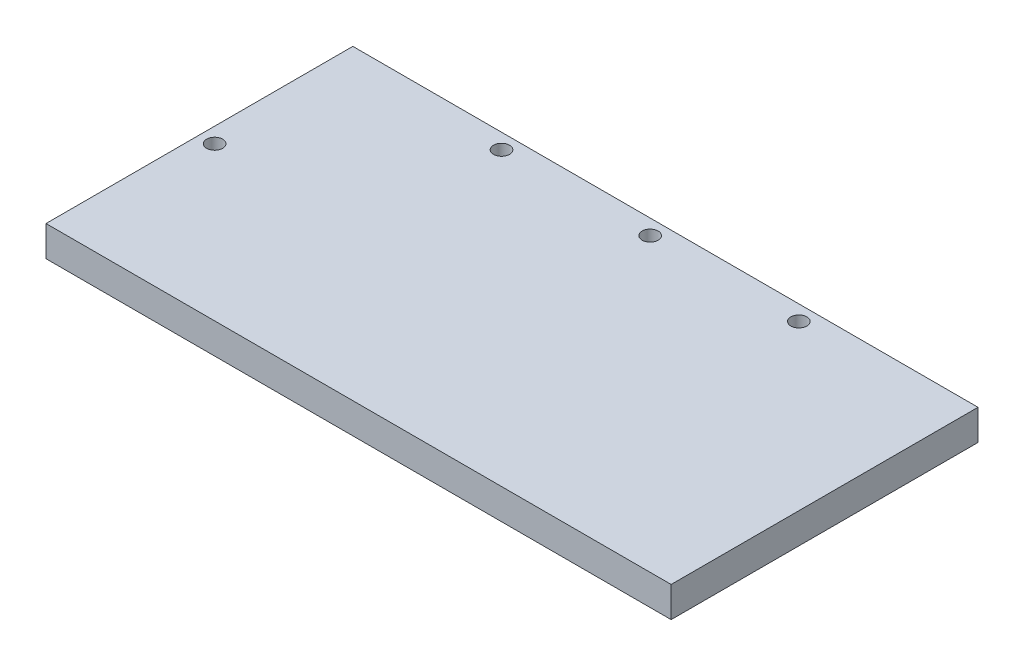
SolidWorks part; units mm, degrees
ref_plane "Front Plane" through (0, 0, 0) normal (0, 0, 1) x (1, 0, 0)
ref_plane "Top Plane" through (0, 0, 0) normal (0, 1, 0) x (1, 0, 0)
ref_plane "Right Plane" through (0, 0, 0) normal (1, 0, 0) x (0, 0, -1)
sketch "Sketch1" plane through (0, 0, 0) normal (0, 1, 0) x (1, 0, 0)
  line L0 (0, 40.25) -> (0, -40.25) construction
  line L1 (-82, 40.25) -> (82, 40.25)
  line L2 (-82, 40.25) -> (-82, -40.25)
  line L3 (-82, -40.25) -> (82, -40.25)
  line L4 (82, 40.25) -> (82, -40.25)
  line L5 (-82, 40.25) -> (82, -40.25) construction
  line L6 (-82, -40.25) -> (82, 40.25) construction
  line L7 (-82, 40.25) -> (-74, 40.25)
  line L8 (-82, 40.25) -> (-82, -40.25)
  line L9 (-82, -40.25) -> (-74, -40.25)
  line L10 (-74, 40.25) -> (-74, -40.25)
  line L11 (74, 36.25) -> (-74, 36.25) construction
  line L12 (-74, 40.25) -> (74, 40.25)
  line L13 (-74, 40.25) -> (-74, 32.25)
  line L14 (-74, 32.25) -> (74, 32.25)
  line L15 (74, 40.25) -> (74, 32.25)
  line L16 (-82, 0) -> (-74, 0) construction
  circle A0 centre (0, 36.25) radius 2.1
  circle A1 centre (39, 36.25) radius 2.1
  circle A2 centre (-39, 36.25) radius 2.1
  circle A3 centre (-78, 0) radius 2.1
  point P0 (0, 0)
  point P10 (-82, 0)
  point P11 (-74, 0)
  dimension "D6" = 4.2
  dimension "D9" = 4.2
  dimension "D1" = 80.5
  dimension "D2" = 164
  dimension "D3" = 8
  dimension "D4" = 8
  dimension "D5" = 8
  dimension "D8" = 39
  dimension "D7" = 2
extrude "Boss-Extrude1" add sketch "Sketch1" along normal blind 8 contours L10 L1 L2 L3 | L15 L1 L10 L14 A0 A1 A2 | L1 L15 L14 L10 L3 L4
